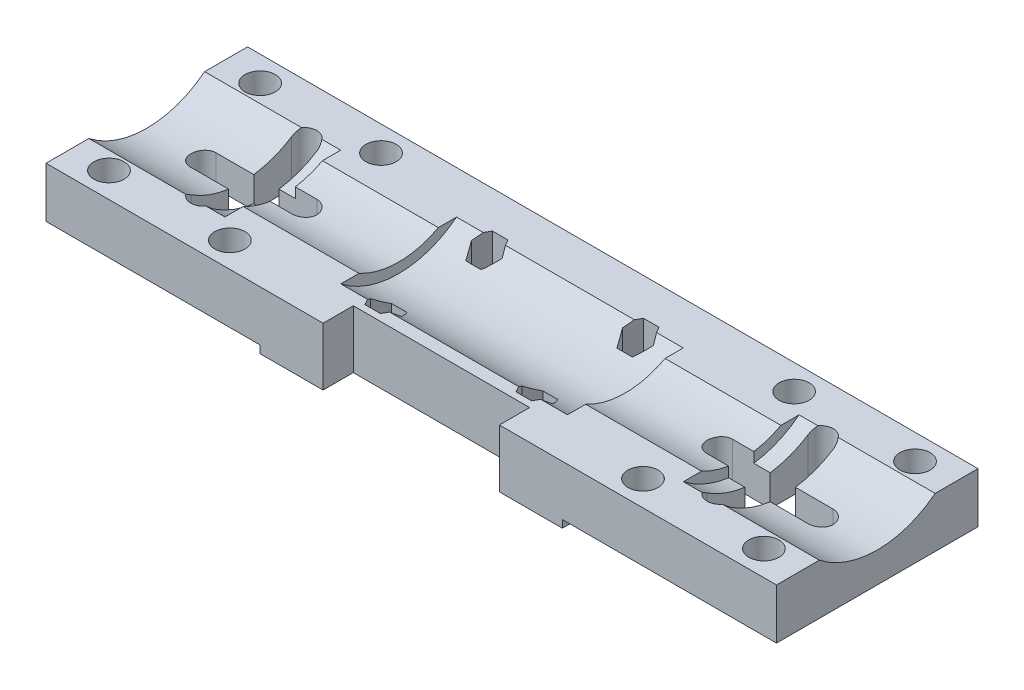
SolidWorks part; units mm, degrees
ref_plane "前视基准面" through (0, 0, 0) normal (0, 0, 1) x (1, 0, 0)
ref_plane "上视基准面" through (0, 0, 0) normal (0, 1, 0) x (1, 0, 0)
ref_plane "右视基准面" through (0, 0, 0) normal (1, 0, 0) x (0, 0, -1)
sketch "草图1" plane through (0, 0, 0) normal (1, 0, 0) x (0, 0, -1)
  line L6 (-20, 10) -> (-20, 0)
  line L7 (-20, 0) -> (20, 0)
  line L8 (20, 10) -> (20, 0)
  line L9 (-20, 24.5) -> (20, 0) construction
  line L10 (-20, 0) -> (20, 24.5) construction
  line L12 (20, 10) -> (11.4891, 10)
  line L13 (0, 0) -> (0, 30.464) construction
  line L14 (-20, 10) -> (-11.4891, 10)
  arc A2 (-11.4891, 10) -> (11.4891, 10) centre (0, 24.5) ccw
  point P0 (0, 12.25)
  dimension "D1" = 18.5
  dimension "D4" = 10
  dimension "D2" = 40
  dimension "D5" = 24.5
extrude "凸台-拉伸1" add sketch "草图1" along normal blind 145
sketch "草图2" plane through (0, 0, 0) normal (0, -1, 0) x (1, 0, 0)
  line L0 (0, 0) -> (177.1338, 0) construction
  line L1 (145, 20) -> (145, -20) construction
  line L2 (137.5, -15) -> (113.5, -15) construction
  line L3 (137.5, -15) -> (137.5, 15) construction
  line L4 (137.5, 15) -> (113.5, 15) construction
  line L5 (113.5, -15) -> (113.5, 15) construction
  line L6 (137.5, -15) -> (113.5, 15) construction
  line L7 (137.5, 15) -> (113.5, -15) construction
  line L8 (72.5, -20) -> (72.5, 20) construction
  line L9 (145, -20) -> (0, -20) construction
  line L10 (145, 20) -> (0, 20) construction
  line L11 (7.5, 15) -> (31.5, -15) construction
  line L12 (7.5, -15) -> (31.5, 15) construction
  line L13 (31.5, -15) -> (31.5, 15) construction
  line L14 (7.5, 15) -> (31.5, 15) construction
  line L15 (7.5, -15) -> (7.5, 15) construction
  line L16 (7.5, -15) -> (31.5, -15) construction
  line L17 (145, 0) -> (-32.1338, 0) construction
  circle A0 centre (137.5, -15) radius 3
  circle A1 centre (113.5, -15) radius 3
  circle A2 centre (113.5, 15) radius 3
  circle A3 centre (137.5, 15) radius 3
  circle A4 centre (7.5, 15) radius 3
  circle A5 centre (31.5, 15) radius 3
  circle A6 centre (31.5, -15) radius 3
  circle A7 centre (7.5, -15) radius 3
  point P3 (125.5, 0)
  point P30 (19.5, 0)
  dimension "D4" = 6
  dimension "D5" = 6
  dimension "D1" = 24
  dimension "D2" = 30
  dimension "D3" = 7.5
extrude "切除-拉伸1" cut sketch "草图2" against normal through all
ref_plane "基准面1" through (27, 0, 0) normal (1, 0, 0) x (0, 0, -1)
sketch "草图3" plane through (27, 0, 0) normal (1, 0, 0) x (0, 0, -1)
  line L2 (11.4891, 10) -> (7.874, 10)
  line L3 (-7.874, 10) -> (-11.4891, 10)
  arc A0 (-11.4891, 10) -> (11.4891, 10) centre (0, 24.5) ccw construction
  arc A1 (-11.4891, 10) -> (11.4891, 10) centre (0, 24.5) ccw
  arc A2 (-7.874, 10) -> (7.874, 10) centre (0, 24.5) ccw
  dimension "D1" = 33
extrude "凸台-拉伸2" add sketch "草图3" along normal blind 23
ref_plane "基准面2" through (72.5, 0, 0) normal (1, 0, 0) x (0, 0, -1)
mirror "镜向1" about plane through (72.5, 0, 0) normal (1, 0, 0) of "凸台-拉伸2"
sketch "草图4" plane through (0, 0, 0) normal (0, -1, 0) x (1, 0, 0)
  line L0 (0, 0) -> (167.0817, 0) construction
  line L1 (72.5, 20) -> (72.5, -20) construction
  line L2 (145, 20) -> (0, 20) construction
  line L3 (145, -20) -> (0, -20) construction
  line L5 (42.5, 20) -> (102.5, 20)
  line L6 (42.5, 20) -> (42.5, -20)
  line L7 (42.5, -20) -> (102.5, -20)
  line L8 (102.5, 20) -> (102.5, -20)
  line L9 (42.5, 20) -> (102.5, -20) construction
  line L10 (42.5, -20) -> (102.5, 20) construction
  point P9 (72.5, 0)
  dimension "D1" = 60
extrude "凸台-拉伸3" add sketch "草图4" along normal blind 1.5
sketch "草图5" plane through (0, -1.5, 0) normal (0, -1, 0) x (1, 0, 0)
  line L0 (0, 0) -> (185.206, 0) construction
  line L1 (72.5, 20) -> (72.5, -44.7016) construction
  line L2 (102.5, 20) -> (42.5, 20) construction
  line L4 (57.5, 10) -> (87.5, 10) construction
  line L5 (57.5, 10) -> (57.5, -10) construction
  line L6 (57.5, -10) -> (87.5, -10) construction
  line L7 (87.5, 10) -> (87.5, -10) construction
  line L8 (57.5, 10) -> (87.5, -10) construction
  line L9 (57.5, -10) -> (87.5, 10) construction
  circle A0 centre (57.5, 10) radius 1.65
  circle A1 centre (87.5, 10) radius 1.65
  circle A2 centre (57.5, 10) radius 1.65
  circle A3 centre (87.5, 10) radius 1.65
  circle A4 centre (57.5, 10) radius 1.65
  circle A5 centre (87.5, 10) radius 1.65
  circle A6 centre (87.5, -10) radius 1.65
  circle A7 centre (57.5, -10) radius 1.65
  point P7 (72.5, 0)
  dimension "D3" = 3.3
  dimension "D1" = 30
  dimension "D2" = 20
extrude "切除-拉伸2" cut sketch "草图5" against normal through all contours A0 | A7 | A6 | A1
sketch "草图6" plane through (0, 10, 0) normal (0, 1, 0) x (1, 0, 0)
  line L1 (60.56, 10) -> (59.03, 12.65)
  line L2 (59.03, 12.65) -> (55.97, 12.65)
  line L3 (55.97, 12.65) -> (54.44, 10)
  line L4 (54.44, 10) -> (55.97, 7.35)
  line L5 (55.97, 7.35) -> (59.03, 7.35)
  line L6 (59.03, 7.35) -> (60.56, 10)
  line L7 (90.56, 10) -> (89.03, 12.65)
  line L8 (89.03, 12.65) -> (85.97, 12.65)
  line L9 (85.97, 12.65) -> (84.44, 10)
  line L10 (84.44, 10) -> (85.97, 7.35)
  line L11 (85.97, 7.35) -> (89.03, 7.35)
  line L12 (89.03, 7.35) -> (90.56, 10)
  line L13 (60.56, -10) -> (59.03, -7.35)
  line L14 (59.03, -7.35) -> (55.97, -7.35)
  line L15 (55.97, -7.35) -> (54.44, -10)
  line L16 (54.44, -10) -> (55.97, -12.65)
  line L17 (55.97, -12.65) -> (59.03, -12.65)
  line L18 (59.03, -12.65) -> (60.56, -10)
  line L19 (90.56, -10) -> (89.03, -7.35)
  line L20 (89.03, -7.35) -> (85.97, -7.35)
  line L21 (85.97, -7.35) -> (84.44, -10)
  line L22 (84.44, -10) -> (85.97, -12.65)
  line L23 (85.97, -12.65) -> (89.03, -12.65)
  line L24 (89.03, -12.65) -> (90.56, -10)
  circle A0 centre (57.5, 10) radius 2.65 construction
  circle A1 centre (87.5, 10) radius 2.65 construction
  circle A2 centre (57.5, -10) radius 2.65 construction
  circle A3 centre (87.5, -10) radius 2.65 construction
  dimension "D1" = 5.3
  dimension "D2" = 5.3
  dimension "D3" = 5.3
  dimension "D4" = 5.3
extrude "切除-拉伸3" cut sketch "草图6" against normal blind 7
sketch "草图8" plane through (0, 10, 0) normal (0, 1, 0) x (1, 0, 0)
  line L0 (72.5, 20) -> (72.5, -27.6772) construction
  line L1 (145, 20) -> (0, 20) construction
  line L2 (145, -20) -> (0, -20) construction
  line L3 (55, -14) -> (90, -14)
  line L4 (55, -14) -> (55, -20)
  line L5 (55, -20) -> (90, -20)
  line L6 (90, -14) -> (90, -20)
  line L7 (55, -14) -> (90, -20) construction
  line L8 (55, -20) -> (90, -14) construction
  point P4 (72.5, -17)
  dimension "D1" = 6
  dimension "D2" = 35
extrude "切除-拉伸5" cut sketch "草图8" against normal through all
sketch "草图9" plane through (0, 0, 0) normal (0, -1, 0) x (1, 0, 0)
  line L0 (133.75, 0) -> (113.75, 0) construction
  line L1 (133.75, -2.5) -> (126.25, -2.5)
  line L2 (133.75, 2.5) -> (126.25, 2.5)
  line L3 (145, 20) -> (102.5, 20) construction
  line L4 (123.75, 10) -> (123.75, -10) construction
  line L5 (126.25, 10) -> (126.25, 2.5)
  line L6 (121.25, 10) -> (121.25, 2.5)
  line L7 (72.5, -20) -> (72.5, 14) construction
  line L8 (42.5, -20) -> (102.5, -20) construction
  line L9 (90, 14) -> (55, 14) construction
  line L10 (121.25, -2.5) -> (113.75, -2.5)
  line L11 (121.25, 2.5) -> (113.75, 2.5)
  line L12 (126.25, -2.5) -> (126.25, -10)
  line L13 (121.25, -2.5) -> (121.25, -10)
  line L14 (21.25, 10) -> (21.25, -10) construction
  line L15 (11.25, 0) -> (31.25, 0) construction
  line L16 (23.75, -2.5) -> (23.75, -10)
  line L17 (18.75, -2.5) -> (18.75, -10)
  line L18 (23.75, 2.5) -> (31.25, 2.5)
  line L19 (23.75, -2.5) -> (31.25, -2.5)
  line L20 (23.75, 10) -> (23.75, 2.5)
  line L21 (18.75, 10) -> (18.75, 2.5)
  line L22 (11.25, 2.5) -> (18.75, 2.5)
  line L23 (11.25, -2.5) -> (18.75, -2.5)
  arc A0 (133.75, -2.5) -> (133.75, 2.5) centre (133.75, 0) ccw
  arc A1 (113.75, 2.5) -> (113.75, -2.5) centre (113.75, 0) ccw
  arc A2 (126.25, 10) -> (121.25, 10) centre (123.75, 10) ccw
  arc A3 (121.25, -10) -> (126.25, -10) centre (123.75, -10) ccw
  arc A4 (23.75, -10) -> (18.75, -10) centre (21.25, -10) cw
  arc A5 (18.75, 10) -> (23.75, 10) centre (21.25, 10) cw
  arc A6 (31.25, 2.5) -> (31.25, -2.5) centre (31.25, 0) cw
  arc A7 (11.25, -2.5) -> (11.25, 2.5) centre (11.25, 0) cw
  point P2 (123.75, 0)
  point P12 (123.75, 20)
  point P13 (123.75, 0)
  point P45 (21.25, 0)
  dimension "D2" = 2.5
  dimension "D3" = 2.5
  dimension "D1" = 20
  dimension "D4" = 20
extrude "切除-拉伸6" cut sketch "草图9" against normal through all
